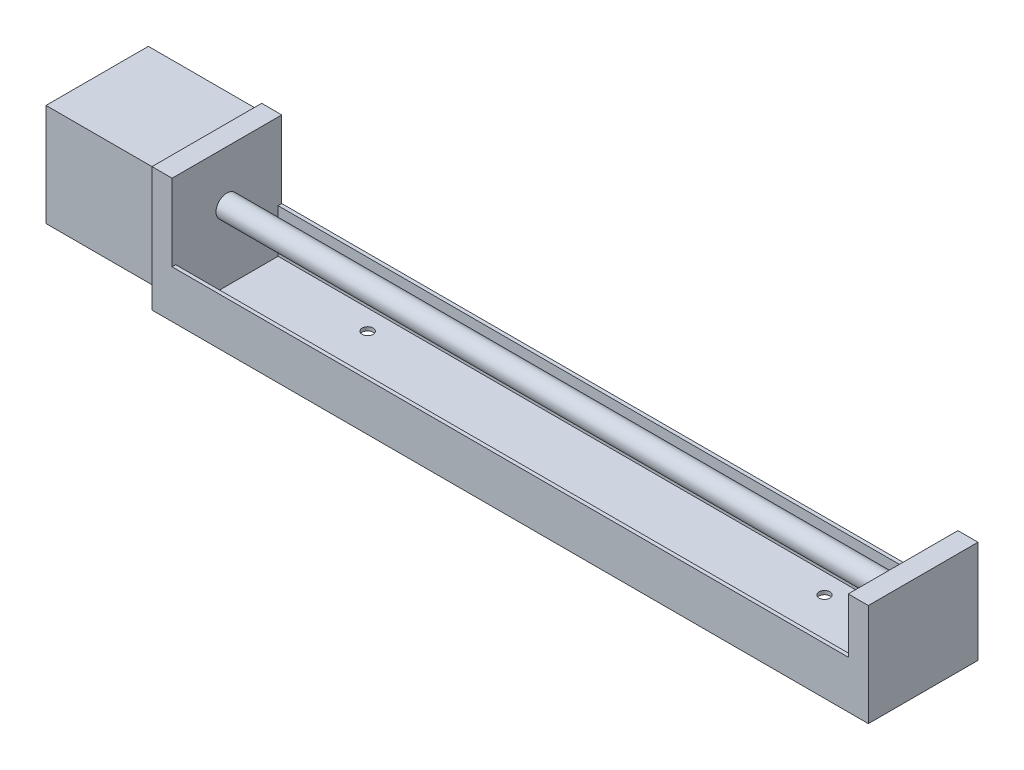
SolidWorks part; units mm, degrees
material "普通碳钢"
ref_plane "前视基准面" through (0, 0, 0) normal (0, 0, 1) x (1, 0, 0)
ref_plane "上视基准面" through (0, 0, 0) normal (0, 1, 0) x (1, 0, 0)
ref_plane "右视基准面" through (0, 0, 0) normal (1, 0, 0) x (0, 0, -1)
other "Configuration Table"
sketch "草图1" plane through (0, 0, 0) normal (0, 0, 1) x (1, 0, 0)
  line L1 (-15, -14) -> (15, -14)
  line L2 (-15, -14) -> (-15, 14)
  line L3 (-15, 14) -> (15, 14)
  line L4 (15, -14) -> (15, 14)
  line L5 (-15, -14) -> (15, 14) construction
  line L6 (-15, 14) -> (15, -14) construction
  point P0 (0, 0)
  dimension "D1" = 28
  dimension "D2" = 30
extrude "凸台-拉伸1" add sketch "草图1" along normal mid plane 28
sketch "草图2" plane through (15, 0, 0) normal (1, 0, 0) x (0, 0, -1)
  line L4 (-14, 14) -> (14, 14) construction
  line L5 (-15, 15) -> (-15, -19)
  line L6 (-15, -19) -> (15, -19)
  line L7 (15, -19) -> (15, 15)
  line L13 (15, 15) -> (-15, 15)
  line L16 (-14, -14) -> (-14, 14) construction
  line L17 (14, -14) -> (14, 14) construction
  dimension "D2" = 1
  dimension "D1" = 1
  dimension "D3" = 1
  dimension "D4" = 34
extrude "凸台-拉伸2" add sketch "草图2" along normal blind 5.5
sketch "草图3" plane through (20.5, 0, 0) normal (1, 0, 0) x (0, 0, -1)
  line L0 (15, -19) -> (15, 15) construction
  line L1 (-15, -19) -> (15, -19)
  line L2 (-15, -19) -> (-15, -6)
  line L3 (-15, -6) -> (-14, -6)
  line L4 (15, -19) -> (15, -6)
  line L5 (-15, -19) -> (15, -6) construction
  line L6 (-15, -6) -> (15, -19) construction
  line L7 (-15, 15) -> (-15, -19) construction
  line L8 (-15, -19) -> (15, -19) construction
  line L9 (-14, -6) -> (-14, -18)
  line L10 (-14, -18) -> (14, -18)
  line L11 (14, -18) -> (14, -6)
  line L12 (14, -6) -> (15, -6)
  point P0 (0, -12.5)
  dimension "D1" = 13
  dimension "D2" = 1
  dimension "D3" = 1
  dimension "D4" = 1
extrude "凸台-拉伸3" add sketch "草图3" along normal blind 185
sketch "草图4" plane through (205.5, 0, 0) normal (1, 0, 0) x (0, 0, -1)
  line L0 (15, -6) -> (15, 15) construction
  line L1 (-15, -19) -> (15, -19)
  line L2 (-15, -19) -> (-15, 9)
  line L3 (-15, 9) -> (15, 9)
  line L4 (15, -19) -> (15, 9)
  dimension "D1" = 28
extrude "凸台-拉伸4" add sketch "草图4" along normal blind 5.5
sketch "草图5" plane through (211, 0, 0) normal (1, 0, 0) x (0, 0, -1)
  line L0 (-15, -19) -> (15, -19) construction
  line L1 (0, -1000) -> (0, 49000) construction
  circle A0 centre (0, 1) radius 3
  dimension "D2" = 6
  dimension "D1" = 20
extrude "凸台-拉伸5" add sketch "草图5" against normal up to surface (190.5 mm away) up to face at (20.5, -3.75, 0)
sketch "Sketch1" plane through (0, -19, 0) normal (0, -1, 0) x (1, 0, 0)
  line L5 (113, 15) -> (113, -15) construction
  line L8 (211, 15) -> (15, 15) construction
  line L9 (211, -15) -> (15, -15) construction
  line L11 (50.5, -8.5) -> (175.5, -8.5) construction
  line L12 (50.5, -8.5) -> (50.5, 8.5) construction
  line L13 (50.5, 8.5) -> (175.5, 8.5) construction
  line L14 (175.5, -8.5) -> (175.5, 8.5) construction
  line L15 (50.5, -8.5) -> (175.5, 8.5) construction
  line L16 (50.5, 8.5) -> (175.5, -8.5) construction
  circle A0 centre (50.5, 8.5) radius 1.5
  circle A1 centre (175.5, 8.5) radius 1.5
  circle A2 centre (175.5, -8.5) radius 1.5
  circle A3 centre (50.5, -8.5) radius 1.5
  point P6 (113, 0)
  dimension "D3" = 3
  dimension "D4" = 3
  dimension "D5" = 3
  dimension "D6" = 3
  dimension "D1" = 125
  dimension "D2" = 17
extrude "Cut-Extrude1" cut sketch "Sketch1" against normal blind 10
